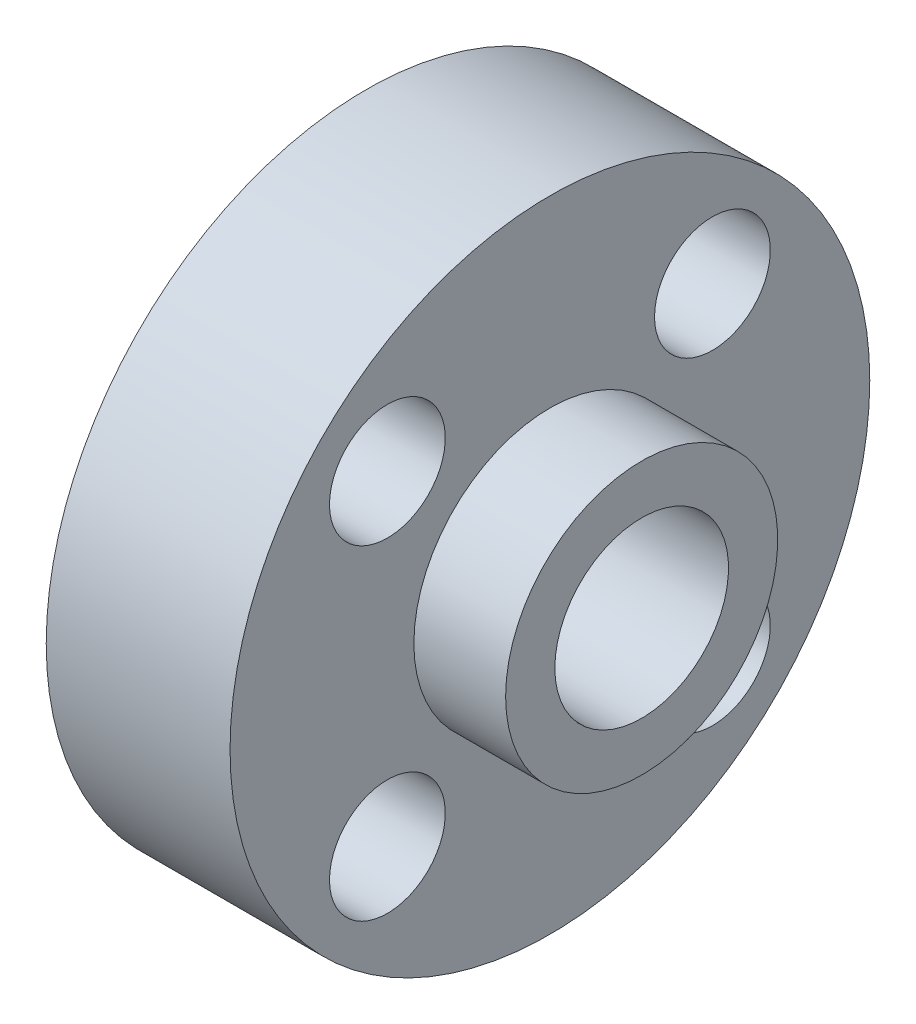
SolidWorks part; units mm, degrees
ref_plane "Plan de face" through (0, 0, 0) normal (0, 0, 1) x (1, 0, 0)
ref_plane "Plan de dessus" through (0, 0, 0) normal (0, 1, 0) x (1, 0, 0)
ref_plane "Plan de droite" through (0, 0, 0) normal (1, 0, 0) x (0, 0, -1)
sketch "Esquisse1" plane through (0, 0, 0) normal (0, 1, 0) x (1, 0, 0)
  line L0 (-53.297, 0) -> (66.3939, 0) construction
  line L1 (-40.2001, 0) -> (-40.2001, 4.7)
  line L2 (-40.2001, 4.7) -> (-37.0201, 4.7)
  line L3 (-37.0201, 4.7) -> (-37.0201, 11.05)
  line L4 (-37.0201, 11.05) -> (-30.6701, 11.05)
  line L5 (-30.6701, 11.05) -> (-30.6701, 4.7)
  line L6 (-30.6701, 4.7) -> (-27.5001, 4.7)
  line L7 (-27.5001, 4.7) -> (-27.5001, 0)
  line L8 (-27.5001, 0) -> (-40.2001, 0)
  dimension "D1" = 3.18
  dimension "D2" = 9.53
  dimension "D3" = 12.7
  dimension "D4" = 4.7
  dimension "D5" = 4.7
  dimension "D6" = 11.05
revolve "Révolution1" add sketch "Esquisse1" angle 360 about L0
sketch "Esquisse2" plane through (-40.2001, 0, 0) normal (-1, 0, 0) x (0, 0, 1)
  circle A0 centre (0, 0) radius 3
  dimension "D1" = 6
extrude "Enlèv. mat.-Extru.1" cut sketch "Esquisse2" against normal through all
sketch "Esquisse3" plane through (-37.0201, 0, 0) normal (-1, 0, 0) x (0, 0, 1)
  line L0 (0, 0) -> (-5.6144, 5.6144) construction
  line L1 (0, -6.985) -> (0, 6.985) construction
  circle A0 centre (-5.6144, 5.6144) radius 2
  dimension "D1" = 4
  dimension "D2" = 45
extrude "Enlèv. mat.-Extru.2" cut sketch "Esquisse3" against normal blind 10
pattern_circular "Répétition circulaire1" count 4 every 90 about axis through (0, 0, 0) along (1, 0, 0) of "Enlèv. mat.-Extru.2"
sketch "Esquisse5" plane through (0, 0, 0) normal (0, 0, 1) x (1, 0, 0)
  line L2 (-43.9255, 0) -> (-22.3265, 0) construction
  line L4 (-30.6701, -11.05) -> (-30.6701, 11.05) construction
  circle A0 centre (-33.8451, 0) radius 2.5
  dimension "D1" = 5
  dimension "D2" = 0
  dimension "D3" = 3.175
extrude "Enlèv. mat.-Extru.3" cut sketch "Esquisse5" against normal through all contours A0
